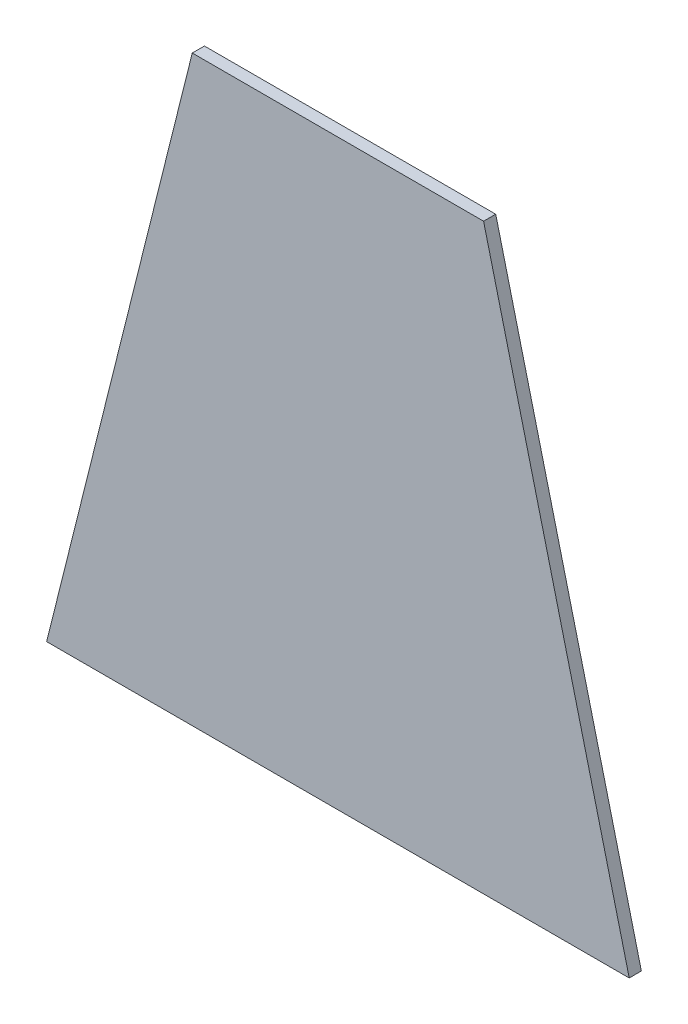
SolidWorks part; units mm, degrees
material "6061-T6 (SS)"
ref_plane "Front Plane" through (0, 0, 0) normal (0, 0, 1) x (1, 0, 0)
ref_plane "Top Plane" through (0, 0, 0) normal (0, 1, 0) x (1, 0, 0)
ref_plane "Right Plane" through (0, 0, 0) normal (1, 0, 0) x (0, 0, -1)
sketch "Sketch2" plane through (0, 0, 0) normal (0, 0, 1) x (1, 0, 0)
  line L0 (0, 0) -> (152.4, 0)
  line L1 (76.2, 0) -> (76.2, 152.4) construction
  line L2 (38.1, 152.4) -> (114.3, 152.4)
  line L3 (38.1, 152.4) -> (0, 0)
  line L4 (114.3, 152.4) -> (152.4, 0)
  point P7 (76.2, 152.4)
  dimension "D1" = 152.4
  dimension "D2" = 76.2
  dimension "D3" = 152.4
extrude "Boss-Extrude1" add sketch "Sketch2" along normal blind 3.175
